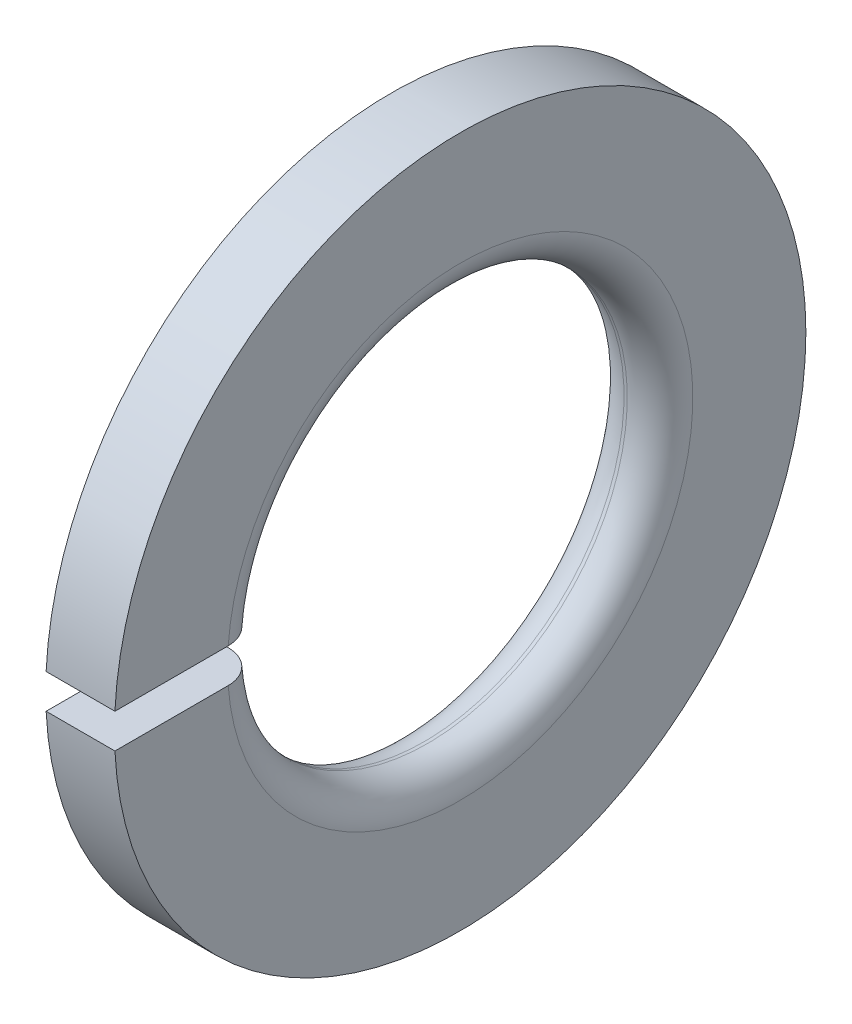
SolidWorks part; units mm, degrees
ref_plane "Plane1" through (0, 0, 0) normal (0, 0, 1) x (1, 0, 0)
ref_plane "Plane2" through (0, 0, 0) normal (0, 1, 0) x (1, 0, 0)
ref_plane "Plane3" through (0, 0, 0) normal (1, 0, 0) x (0, 0, -1)
sketch "Sketch1" plane through (0, 0, 0) normal (0, 0, 1) x (1, 0, 0)
  line L0 (-34.925, 0) -> (9.525, 0) construction
  line L1 (0, 7.1) -> (0, 10.55)
  line L2 (0, 10.55) -> (-2.1, 10.55)
  line L3 (-2.1, 10.55) -> (-2.1, 7.1)
  line L4 (-1.1, 6.1) -> (-1, 6.1)
  arc A0 (-1.1, 6.1) -> (-2.1, 7.1) centre (-1.1, 7.1) cw
  arc A1 (0, 7.1) -> (-1, 6.1) centre (-1, 7.1) cw
  point P8 (-2.1, 6.1)
  dimension "Fillet_rad" = 1
  dimension "D1" = 1
  dimension "Thickness" = 2.1
  dimension "Inside_dia" = 12.2
  dimension "Outside_dia" = 21.1
revolve "Base-Revolve" add sketch "Sketch1" angle 360 about L0
sketch "Sketch2" plane through (0, 0, 0) normal (-1, 0, 0) x (0, -1, 0)
  line L0 (-0.525, 0) -> (0.525, 0)
  line L1 (0, 0) -> (0, 12.7) construction
  line L2 (0.525, 0) -> (0.525, 10.761)
  line L3 (0.525, 10.761) -> (-0.525, 10.761)
  line L4 (-0.525, 10.761) -> (-0.525, 0)
  dimension "D1" = 1.05
  dimension "D2" = 10.761
extrude "Gap" cut sketch "Sketch2" along normal through all
equation "\"D1@Sketch1\" = \"Fillet_rad@Sketch1\""
equation "\"D1@Sketch2\" = \"Thickness@Sketch1\" * 0.5"
equation "\"D2@Sketch2\" = \"Outside_dia@Sketch1\" * 0.51"
